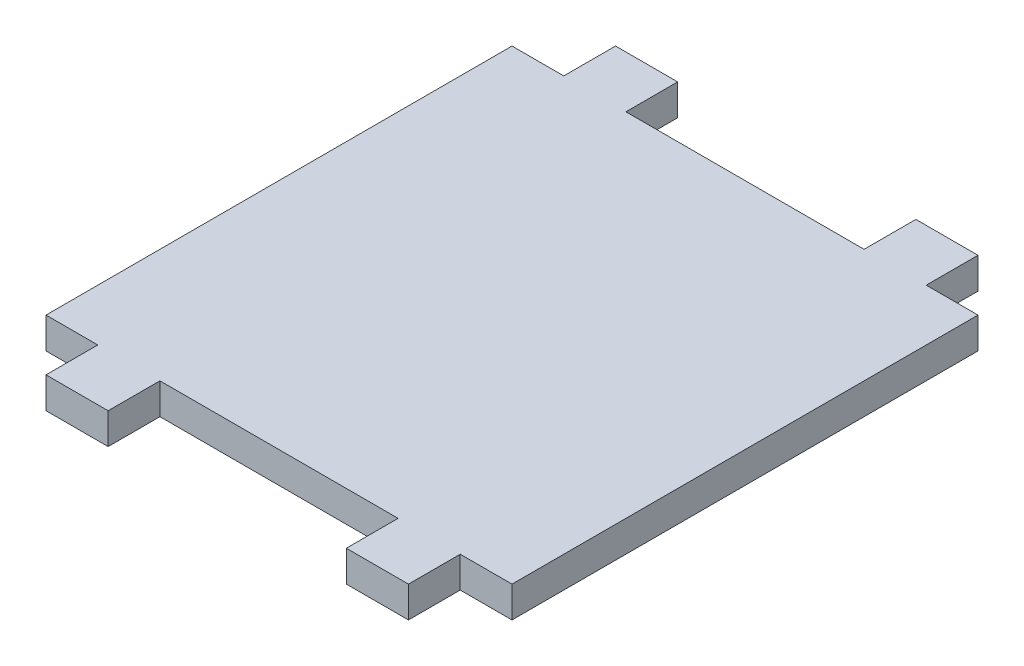
SolidWorks part; units mm, degrees
ref_plane "Alzado" through (0, 0, 0) normal (0, 0, 1) x (1, 0, 0)
ref_plane "Planta" through (0, 0, 0) normal (0, 1, 0) x (1, 0, 0)
ref_plane "Vista lateral" through (0, 0, 0) normal (1, 0, 0) x (0, 0, -1)
sketch "Croquis1" plane through (0, 0, 0) normal (0, 1, 0) x (1, 0, 0)
  line L1 (-22.5, 22.5) -> (22.5, 22.5)
  line L2 (-22.5, 22.5) -> (-22.5, -22.5)
  line L3 (-22.5, -22.5) -> (22.5, -22.5)
  line L4 (22.5, 22.5) -> (22.5, -22.5)
  line L5 (-22.5, 22.5) -> (22.5, -22.5) construction
  line L6 (-22.5, -22.5) -> (22.5, 22.5) construction
  line L7 (-17.5, 22.5) -> (-11.5, 22.5)
  line L8 (-17.5, 22.5) -> (-17.5, 27.5)
  line L9 (-17.5, 27.5) -> (-11.5, 27.5)
  line L10 (-11.5, 22.5) -> (-11.5, 27.5)
  line L11 (11.5, 22.5) -> (17.5, 22.5)
  line L12 (11.5, 22.5) -> (11.5, 27.5)
  line L13 (11.5, 27.5) -> (17.5, 27.5)
  line L14 (17.5, 22.5) -> (17.5, 27.5)
  line L15 (-17.5, -22.5) -> (-11.5, -22.5)
  line L16 (-17.5, -22.5) -> (-17.5, -27.5)
  line L17 (-17.5, -27.5) -> (-11.5, -27.5)
  line L18 (-11.5, -22.5) -> (-11.5, -27.5)
  line L19 (11.5, -22.5) -> (17.5, -22.5)
  line L20 (11.5, -22.5) -> (11.5, -27.5)
  line L21 (11.5, -27.5) -> (17.5, -27.5)
  line L22 (17.5, -22.5) -> (17.5, -27.5)
  point P0 (0, 0)
  dimension "D1" = 45
  dimension "D2" = 45
  dimension "D3" = 5
  dimension "D4" = 5
  dimension "D5" = 5
  dimension "D6" = 5
  dimension "D7" = 6
  dimension "D8" = 6
  dimension "D9" = 6
  dimension "D10" = 6
  dimension "D11" = 5
  dimension "D12" = 5
  dimension "D13" = 5
  dimension "D14" = 5
extrude "Saliente-Extruir1" add sketch "Croquis1" along normal blind 3 contours L4 L1 L2 L3 | L1 L10 L9 L8 | L1 L14 L13 L12 | L22 L3 L20 L21 | L18 L3 L16 L17
